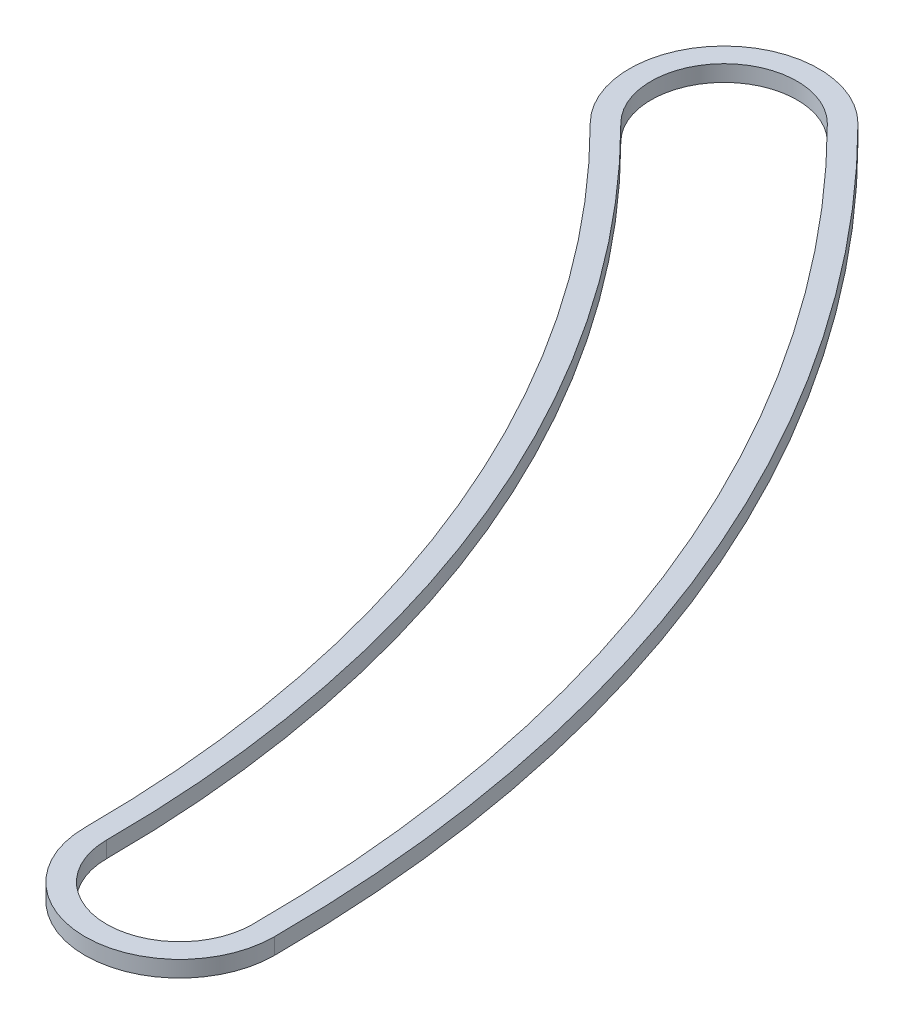
SolidWorks part; units mm, degrees
material "NBR"
ref_plane "Front Plane" through (0, 0, 0) normal (0, 0, 1) x (1, 0, 0)
ref_plane "Top Plane" through (0, 0, 0) normal (0, 1, 0) x (1, 0, 0)
ref_plane "Right Plane" through (0, 0, 0) normal (1, 0, 0) x (0, 0, -1)
sketch "Sketch1" plane through (0, 0, 0) normal (0, 1, 0) x (1, 0, 0)
  line L0 (0, 0) -> (43.644, 43.644) construction
  line L1 (0, 0) -> (61.722, 0) construction
  arc A0 (61.722, 0) -> (43.644, 43.644) centre (0, 0) ccw construction
  arc A1 (66.167, 0) -> (46.7871, 46.7871) centre (0, 0) ccw
  arc A2 (57.277, 0) -> (40.501, 40.501) centre (0, 0) ccw
  arc A3 (57.277, 0) -> (66.167, 0) centre (61.722, 0) ccw
  arc A4 (46.7871, 46.7871) -> (40.501, 40.501) centre (43.644, 43.644) ccw
  arc A5 (61.722, 0) -> (43.644, 43.644) centre (0, 0) ccw construction
  arc A6 (65.151, 0) -> (46.0687, 46.0687) centre (0, 0) ccw
  arc A7 (58.293, 0) -> (41.2194, 41.2194) centre (0, 0) ccw
  arc A8 (58.293, 0) -> (65.151, 0) centre (61.722, 0) ccw
  arc A9 (46.0687, 46.0687) -> (41.2194, 41.2194) centre (43.644, 43.644) ccw
  point P4 (57.0237, 23.62)
  point P13 (57.0237, 23.62)
  dimension "D4" = 61.722
  dimension "D3" = 4.445
  dimension "D1" = 45
  dimension "D2" = 1.016
extrude "Boss-Extrude1" add sketch "Sketch1" along normal blind 0.762
equation "\"w\"= 0.04"
equation "\"D2@Sketch1\"=\"w\""
equation "\"D3@Sketch1\"= .185 - .01 '10 thou smaller than channel rad"
